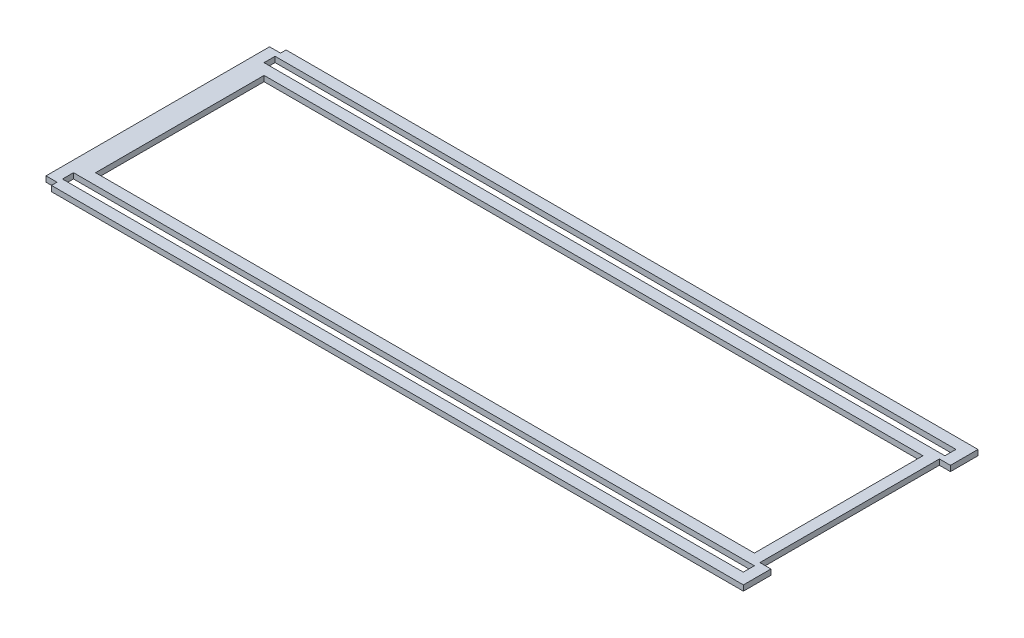
SolidWorks part; units mm, degrees
ref_plane "Front" through (0, 0, 0) normal (0, 0, 1) x (1, 0, 0)
ref_plane "Top" through (0, 0, 0) normal (0, 1, 0) x (1, 0, 0)
ref_plane "Right" through (0, 0, 0) normal (1, 0, 0) x (0, 0, -1)
sketch "Sketch1" plane through (0, 0, 0) normal (0, 1, 0) x (1, 0, 0)
  line L0 (-203.2, 64.6208) -> (-203.2, -64.6208)
  line L1 (-196.85, 67.8212) -> (203.2, 67.8212)
  line L3 (-196.85, -67.8212) -> (203.2, -67.8212)
  line L4 (203.2, 67.8212) -> (203.2, 51.8954)
  line L5 (0, 0) -> (-84.4016, 0) construction
  line L7 (-196.85, 61.4712) -> (196.7992, 61.4712)
  line L9 (-196.85, 55.0704) -> (196.7992, 55.0704)
  line L10 (196.7992, 61.4712) -> (196.7992, 55.0704)
  line L11 (-196.85, -55.0704) -> (196.7992, -55.0704)
  line L13 (-196.85, -61.4712) -> (196.7992, -61.4712)
  line L14 (196.7992, -55.0704) -> (196.7992, -61.4712)
  line L16 (203.2, -51.8954) -> (203.2, -67.8212)
  line L17 (203.2, 51.8954) -> (196.7992, 51.8954)
  line L19 (203.2, -51.8954) -> (196.7992, -51.8954)
  line L20 (196.7992, 51.8954) -> (196.7992, -51.8954)
  line L32 (0, -24.3249) -> (0, 0) construction
  line L37 (-196.85, -55.0704) -> (-196.85, -61.4712)
  line L41 (-196.85, 55.0704) -> (-196.85, 61.4712)
  line L48 (-203.2, -64.6208) -> (-196.85, -64.6208)
  line L49 (-196.85, -67.8212) -> (-196.85, -64.6208)
  line L50 (-203.2, 64.6208) -> (-196.85, 64.6208)
  line L53 (-196.85, 64.6208) -> (-196.85, 67.8212)
  line L54 (-190.4492, 48.7204) -> (190.4492, 48.7204)
  line L55 (-190.4492, 48.7204) -> (-190.4492, -48.7204)
  line L56 (-190.4492, -48.7204) -> (190.4492, -48.7204)
  line L57 (190.4492, 48.7204) -> (190.4492, -48.7204)
  line L58 (-190.4492, 48.7204) -> (190.4492, -48.7204) construction
  line L59 (-190.4492, -48.7204) -> (190.4492, 48.7204) construction
  point P0 (0, 0)
  point P12 (0, 0)
  dimension "D1" = 135.6423
  dimension "D3" = 6.4008
  dimension "D4" = 6.35
  dimension "D5" = 6.35
  dimension "D6" = 6.4008
  dimension "D7" = 3.175
  dimension "D8" = 3.175
  dimension "D2" = 406.4
  dimension "D10" = 67.8212
  dimension "D11" = 203.2
  dimension "D9" = 393.6492
  dimension "D12" = 3.2004
  dimension "D13" = 3.2004
  dimension "D14" = 6.35
  dimension "D15" = 6.35
extrude "Boss-Extrude1" add sketch "Sketch1" along normal blind 3.175
equation "\"D1@Sketch1\"=(5.59025-.25)"
equation "\"D10@Sketch1\"=\"D1@Sketch1\"/2"
